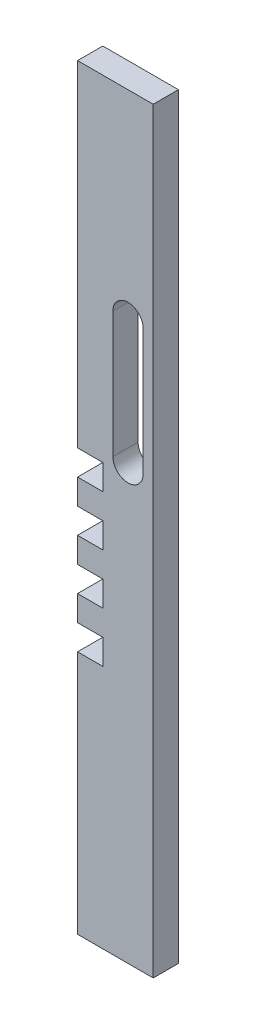
SolidWorks part; units mm, degrees
ref_plane "Plan de face" through (0, 0, 0) normal (0, 0, 1) x (1, 0, 0)
ref_plane "Plan de dessus" through (0, 0, 0) normal (0, 1, 0) x (1, 0, 0)
ref_plane "Plan de droite" through (0, 0, 0) normal (1, 0, 0) x (0, 0, -1)
sketch "Esquisse1" plane through (0, 0, 0) normal (0, 0, 1) x (1, 0, 0)
  line L1 (0, 0) -> (-30, 0)
  line L2 (0, 0) -> (0, 300)
  line L3 (0, 300) -> (-30, 300)
  line L4 (-30, 0) -> (-30, 300)
  dimension "D1" = 30
  dimension "D2" = 300
extrude "Boss.-Extru.1" add sketch "Esquisse1" along normal blind 10
sketch "Esquisse2" plane through (0, 0, 10) normal (0, 0, 1) x (1, 0, 0)
  line L0 (-30, 300) -> (-30, 0) construction
  line L1 (-30, 167) -> (-20, 167)
  line L2 (-30, 167) -> (-30, 157)
  line L3 (-30, 157) -> (-20, 157)
  line L4 (-20, 167) -> (-20, 157)
  line L5 (-30, 0) -> (0, 0) construction
  dimension "D1" = 10
  dimension "D2" = 10
  dimension "D3" = 167
extrude "Enlèv. mat.-Extru.1" cut sketch "Esquisse2" against normal blind 10
pattern_linear "Répétition linéaire1" count 4 spacing 20 along (0, -1, 0) of "Enlèv. mat.-Extru.1"
sketch "Esquisse3" plane through (0, 0, 10) normal (0, 0, 1) x (1, 0, 0)
  line L0 (-4, 171) -> (-4, 221)
  line L1 (-16, 221) -> (-16, 171)
  line L2 (0, 0) -> (0, 300) construction
  line L4 (-30, 227) -> (0, 227) construction
  line L5 (-30, 300) -> (-30, 167) construction
  line L6 (-30, 0) -> (0, 0) construction
  arc A0 (-16, 221) -> (-4, 221) centre (-10, 221) cw
  arc A1 (-16, 171) -> (-4, 171) centre (-10, 171) ccw
  dimension "D3" = 12
  dimension "D1" = 4
  dimension "D2" = 50
  dimension "D4" = 227
extrude "Enlèv. mat.-Extru.2" cut sketch "Esquisse3" against normal blind 10
